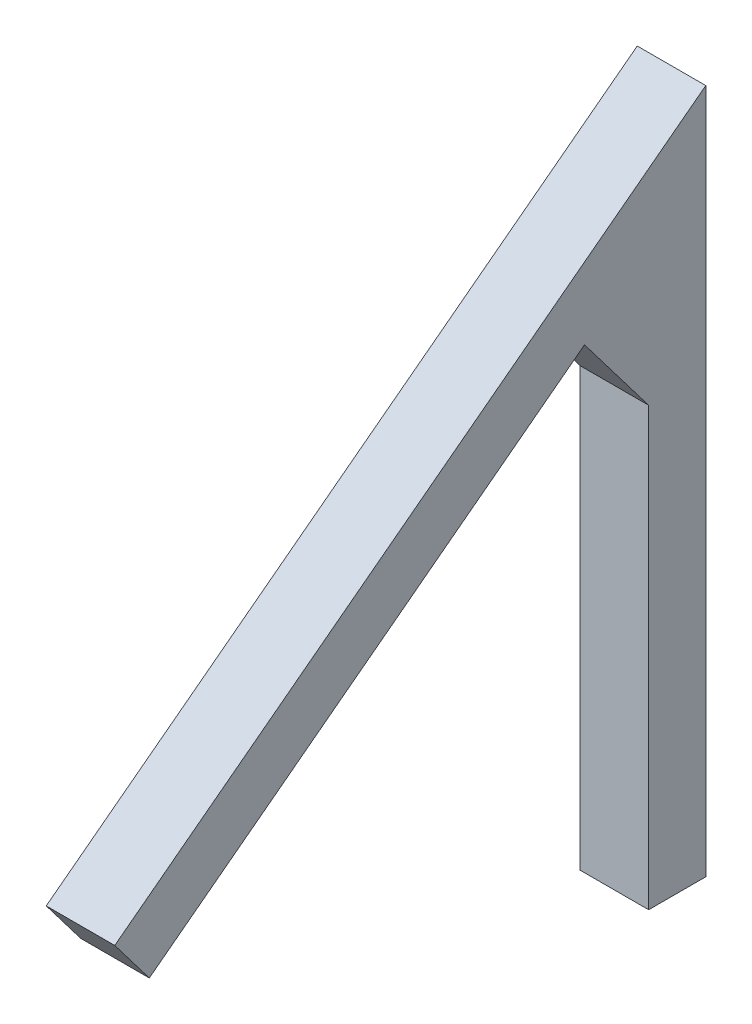
SolidWorks part; units mm, degrees
ref_plane "Front Plane" through (0, 0, 0) normal (0, 0, 1) x (1, 0, 0)
ref_plane "Top Plane" through (0, 0, 0) normal (0, 1, 0) x (1, 0, 0)
ref_plane "Right Plane" through (0, 0, 0) normal (1, 0, 0) x (0, 0, -1)
sketch "Sketch1" plane through (0, 0, 0) normal (1, 0, 0) x (0, 0, -1)
  line L0 (0, -14.9683) -> (0, 51.854) construction
  line L1 (0, -14.9683) -> (0, 45.0317)
  line L2 (0, 45.0317) -> (-51.7505, 5.7013)
  line L3 (-51.7505, 5.7013) -> (-48.7251, 1.7205)
  line L4 (-48.7251, 1.7205) -> (-10.619, 30.6811)
  line L5 (-5, 23.2877) -> (-5, -14.9683)
  line L6 (-5, -14.9683) -> (0, -14.9683)
  line L7 (-5, 23.2877) -> (-10.619, 30.6811)
  point P7 (0, 0)
  dimension "D1" = 65
  dimension "D2" = 5
  dimension "D3" = 5
  dimension "D4" = 60
extrude "Boss-Extrude1" add sketch "Sketch1" along normal blind 6
